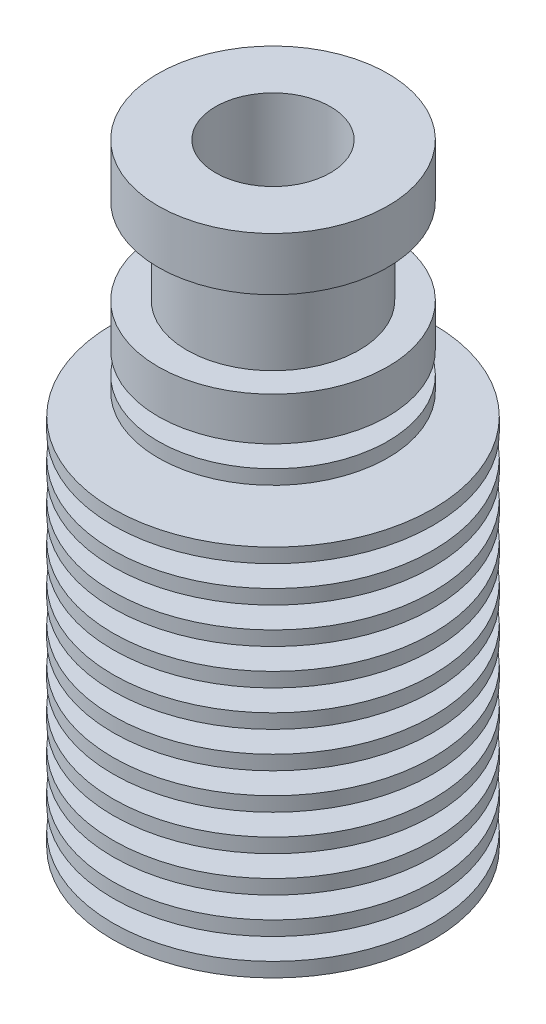
SolidWorks part; units mm, degrees
material "1060 Alloy"
ref_plane "Front Plane" through (0, 0, 0) normal (0, 0, 1) x (1, 0, 0)
ref_plane "Top Plane" through (0, 0, 0) normal (0, 1, 0) x (1, 0, 0)
ref_plane "Right Plane" through (0, 0, 0) normal (1, 0, 0) x (0, 0, -1)
sketch "Sketch1" plane through (0, 0, 0) normal (0, 0, 1) x (1, 0, 0)
  line L0 (0, 21.35) -> (0, -21.35) construction
  line L1 (4, 21.35) -> (8, 21.35)
  line L2 (8, 21.35) -> (8, 17.65)
  line L3 (8, 17.65) -> (6, 17.65)
  line L4 (6, 17.65) -> (6, 11.65)
  line L5 (6, 11.65) -> (8, 11.65)
  line L6 (8, 11.65) -> (8, 8.65)
  line L7 (8, 8.65) -> (4.4, 8.65)
  line L8 (4.4, 8.65) -> (4.4, 7.15)
  line L9 (4.4, 7.15) -> (8, 7.15)
  line L10 (8, 7.15) -> (8, 6.15)
  line L11 (8, 6.15) -> (4.4, 6.15)
  line L12 (4.4, 6.15) -> (4.4, 4.65)
  line L13 (4.4, 4.65) -> (11.15, 4.65)
  line L14 (11.15, 4.65) -> (11.15, 3.65)
  line L15 (11.15, 3.65) -> (4.6, 3.65)
  line L16 (4.6, 3.65) -> (4.6, 2.15)
  line L17 (4.6, 2.15) -> (11.15, 2.15)
  line L18 (11.15, 2.15) -> (11.15, 1.15)
  line L19 (11.15, 1.15) -> (4.8, 1.15)
  line L20 (4.8, 1.15) -> (4.8, -0.35)
  line L21 (4.8, -0.35) -> (11.15, -0.35)
  line L22 (11.15, -0.35) -> (11.15, -1.35)
  line L23 (11.15, -1.35) -> (4.95, -1.35)
  line L24 (4.95, -1.35) -> (4.95, -2.85)
  line L25 (4.95, -2.85) -> (11.15, -2.85)
  line L26 (11.15, -2.85) -> (11.15, -3.85)
  line L27 (11.15, -3.85) -> (5.15, -3.85)
  line L28 (5.15, -3.85) -> (5.15, -5.35)
  line L29 (5.15, -5.35) -> (11.15, -5.35)
  line L30 (11.15, -5.35) -> (11.15, -6.35)
  line L31 (11.15, -6.35) -> (5.35, -6.35)
  line L32 (5.35, -6.35) -> (5.35, -7.85)
  line L33 (5.35, -7.85) -> (11.15, -7.85)
  line L34 (11.15, -7.85) -> (11.15, -8.85)
  line L35 (11.15, -8.85) -> (5.5, -8.85)
  line L36 (5.5, -8.85) -> (5.5, -10.35)
  line L37 (5.5, -10.35) -> (11.15, -10.35)
  line L38 (11.15, -10.35) -> (11.15, -11.35)
  line L39 (11.15, -11.35) -> (5.7, -11.35)
  line L40 (5.7, -11.35) -> (5.7, -12.85)
  line L41 (5.7, -12.85) -> (11.15, -12.85)
  line L42 (11.15, -12.85) -> (11.15, -13.85)
  line L43 (11.15, -13.85) -> (5.9, -13.85)
  line L44 (6.05, -16.35) -> (11.15, -16.35)
  line L45 (11.15, -15.35) -> (5.9, -15.35)
  line L46 (11.15, -16.35) -> (11.15, -15.35)
  line L47 (5.9, -15.35) -> (5.9, -13.85)
  line L48 (6.05, -16.35) -> (6.05, -17.85)
  line L49 (6.05, -17.85) -> (11.15, -17.85)
  line L50 (11.15, -18.85) -> (11.15, -17.85)
  line L51 (11.15, -18.85) -> (6.25, -18.85)
  line L52 (6.25, -18.85) -> (6.25, -20.35)
  line L53 (6.25, -20.35) -> (11.15, -20.35)
  line L54 (11.15, -20.35) -> (11.15, -21.35)
  line L55 (11.15, -21.35) -> (3.5, -21.35)
  line L56 (3.5, -21.35) -> (3.5, -6.55)
  line L68 (4, 21.35) -> (4, 15.35)
  line L69 (4, 15.35) -> (2.1, 14.0196)
  line L70 (2.1, 14.0196) -> (2.1, -5.7417)
  line L71 (2.1, -5.7417) -> (3.5, -6.55)
  dimension "D1" = 42.7
  dimension "D2" = 16
  dimension "D3" = 3.7
  dimension "D4" = 6
  dimension "D5" = 3
  dimension "D6" = 1
  dimension "D7" = 22.3
  dimension "D8" = 12.5
  dimension "D9" = 12.1
  dimension "D10" = 12
  dimension "D11" = 8
  dimension "D12" = 6
  dimension "D13" = 125
  dimension "D14" = 4.2
  dimension "D15" = 7
  dimension "D16" = 14.8
  dimension "D17" = 120
  dimension "D18" = 11.8
  dimension "D19" = 11.4
  dimension "D20" = 11
  dimension "D21" = 10.7
  dimension "D22" = 10.3
  dimension "D23" = 9.9
  dimension "D24" = 9.6
  dimension "D25" = 9.2
  dimension "D26" = 8.8
  dimension "D27" = 8.8
revolve "Revolve1" add sketch "Sketch1" angle 360 about L0
